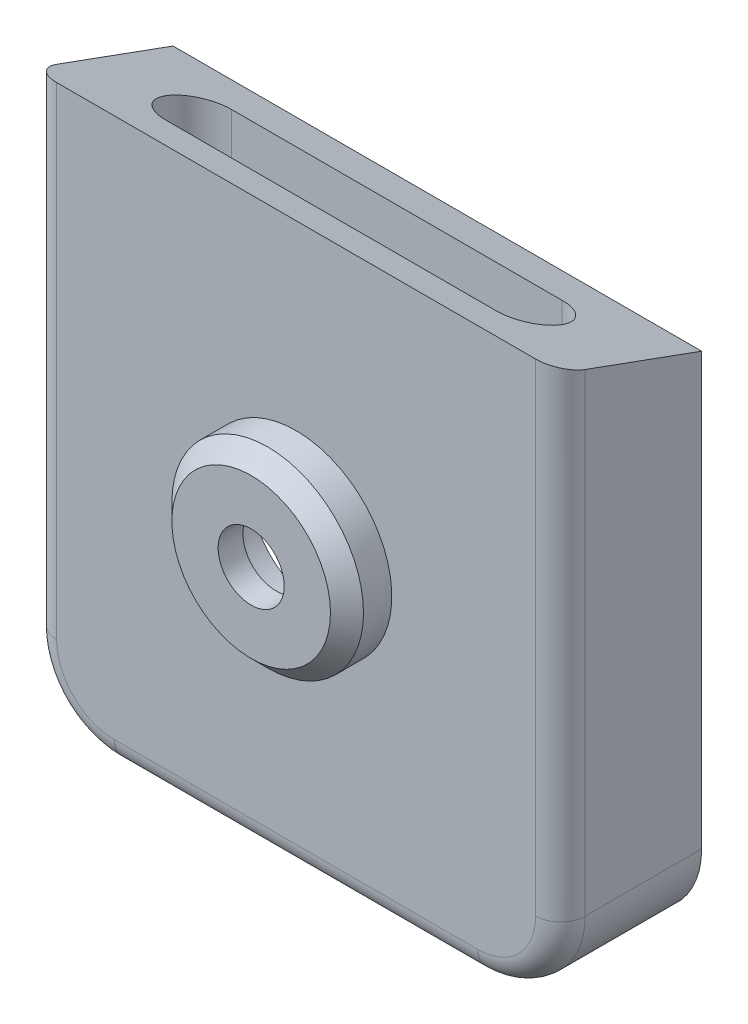
SolidWorks part; units mm, degrees
ref_plane "Front" through (0, 0, 0) normal (0, 0, 1) x (1, 0, 0)
ref_plane "Top" through (0, 0, 0) normal (0, 1, 0) x (1, 0, 0)
ref_plane "Right" through (0, 0, 0) normal (1, 0, 0) x (0, 0, -1)
sketch "Sketch1" plane through (0, 0, 0) normal (0, 0, 1) x (1, 0, 0)
  line L1 (0, 0) -> (32, 0)
  line L2 (0, 0) -> (0, 31.0919)
  line L3 (0, 31.0919) -> (32, 31.0919)
  line L4 (32, 0) -> (32, 31.0919)
  line L8 (0, 31.0919) -> (32, 31.0919) construction
  dimension "D1" = 32
extrude "Boss-Extrude1" add sketch "Sketch1" along normal blind 1.5
fillet "Fillet1" radius 5 2 edges at (32, 0, 0.75) (0, 0, 0.75)
sketch "Sketch2" plane through (0, 0, 0) normal (0, 0, -1) x (-1, 0, 0)
  circle A0 centre (-15.9917, 17.4031) radius 4.3
  circle A1 centre (-15.9917, 17.4031) radius 3.8 construction
  dimension "D1" = 0.5
extrude "Cut-Extrude1" cut sketch "Sketch2" against normal through all
sketch "Sketch3" plane through (0, 0, 1.5) normal (0, 0, 1) x (1, 0, 0)
  circle A0 centre (15.9917, 17.4031) radius 4.3 construction
  circle A1 centre (15.9917, 17.4031) radius 4.3
  circle A2 centre (15.9917, 17.4031) radius 5.8
  dimension "D1" = 1.5
extrude "Boss-Extrude2" add sketch "Sketch3" along normal up to surface (1.213 mm away)
sketch "Sketch4" plane through (0, 0, 2.713) normal (0, 0, 1) x (1, 0, 0)
  circle A0 centre (15.9917, 17.4031) radius 2
  circle A1 centre (15.9917, 17.4031) radius 5.8
  circle A2 centre (15.9917, 17.4031) radius 5.8
  dimension "D2" = 4
  dimension "D1" = 0
extrude "Boss-Extrude3" add sketch "Sketch4" along normal blind 1.5
chamfer "Chamfer1" distance 1 angle 45 1 edges at (21.7917, 17.4031, 4.213)
sketch "Sketch5" plane through (0, 0, 0) normal (0, 0, -1) x (-1, 0, 0)
  line L0 (-32, 5) -> (-32, 31.0919) construction
  line L1 (0, 31.0919) -> (0, 5) construction
  line L2 (-5, 0) -> (-27, 0) construction
  line L3 (-32, 5) -> (-32, 31.0919)
  line L4 (0, 31.0919) -> (0, 5)
  line L5 (-5, 0) -> (-27, 0)
  arc A0 (-32, 5) -> (-27, 0) centre (-27, 5) ccw construction
  arc A1 (-5, 0) -> (0, 5) centre (-5, 5) ccw construction
  arc A2 (-32, 5) -> (-27, 0) centre (-27, 5) ccw
  arc A3 (-5, 0) -> (0, 5) centre (-5, 5) ccw
extrude "Extrude-Thin1" add sketch "Sketch5" along normal up to surface (7.05 mm away) thin
sketch "Sketch6" plane through (32, 0, 0) normal (1, 0, 0) x (0, 0, -1)
  line L0 (7.05, 31.0919) -> (-1.5, 34.2039)
  line L1 (-1.5, 34.2039) -> (-1.5, 31.0919)
  line L2 (-1.5, 5) -> (-1.5, 31.0919) construction
  line L3 (16.3542, 27.7055) -> (7.05, 31.0919) construction
  line L4 (-1.5, 31.0919) -> (7.05, 31.0919)
extrude "Boss-Extrude4" add sketch "Sketch6" against normal up to surface (32 mm away) up to face at (0, 18.046, -2.775)
sketch "Sketch7" plane through (0, 0, 0) normal (0, 0, -1) x (-1, 0, 0)
  line L0 (-1.5, 31.0919) -> (-1.5, 5) construction
  line L1 (-30.5, 31.0919) -> (-1.5, 31.0919)
  line L2 (-30.5, 31.0919) -> (-30.5, 29.2919)
  line L3 (-30.5, 29.2919) -> (-1.5, 29.2919)
  line L4 (-1.5, 31.0919) -> (-1.5, 29.2919)
  dimension "D1" = 1.8
extrude "Boss-Extrude5" add sketch "Sketch7" along normal up to surface (7.05 mm away) up to face at (16, 11.9872, -7.05)
fillet "Fillet2" radius 2 2 edges at (1.5, 29.2919, -3.525) (30.5, 29.2919, -3.525)
sketch "Sketch8" plane through (0, 29.2919, 0) normal (0, -1, 0) x (1, 0, 0)
  line L0 (16, 0) -> (16, -7.05) construction
  line L1 (28.5, 0) -> (3.5, 0) construction
  line L2 (28.5, -7.05) -> (3.5, -7.05) construction
  line L3 (26, -2.6) -> (6, -2.6) construction
  line L4 (26, -4.6) -> (6, -4.6)
  line L5 (26, -0.6) -> (6, -0.6)
  arc A0 (26, -4.6) -> (26, -0.6) centre (26, -2.6) ccw
  arc A1 (6, -0.6) -> (6, -4.6) centre (6, -2.6) ccw
  point P8 (16, -2.6)
  dimension "D1" = 4
  dimension "D2" = 20
  dimension "D3" = 0.6
extrude "Cut-Extrude2" cut sketch "Sketch8" against normal blind 10
fillet "Fillet3" radius 1.5 5 edges at (0, 19.6019, 1.5) (1.4645, 1.4645, 1.5) (16, 0, 1.5) (30.5355, 1.4645, 1.5) (32, 19.6019, 1.5)
